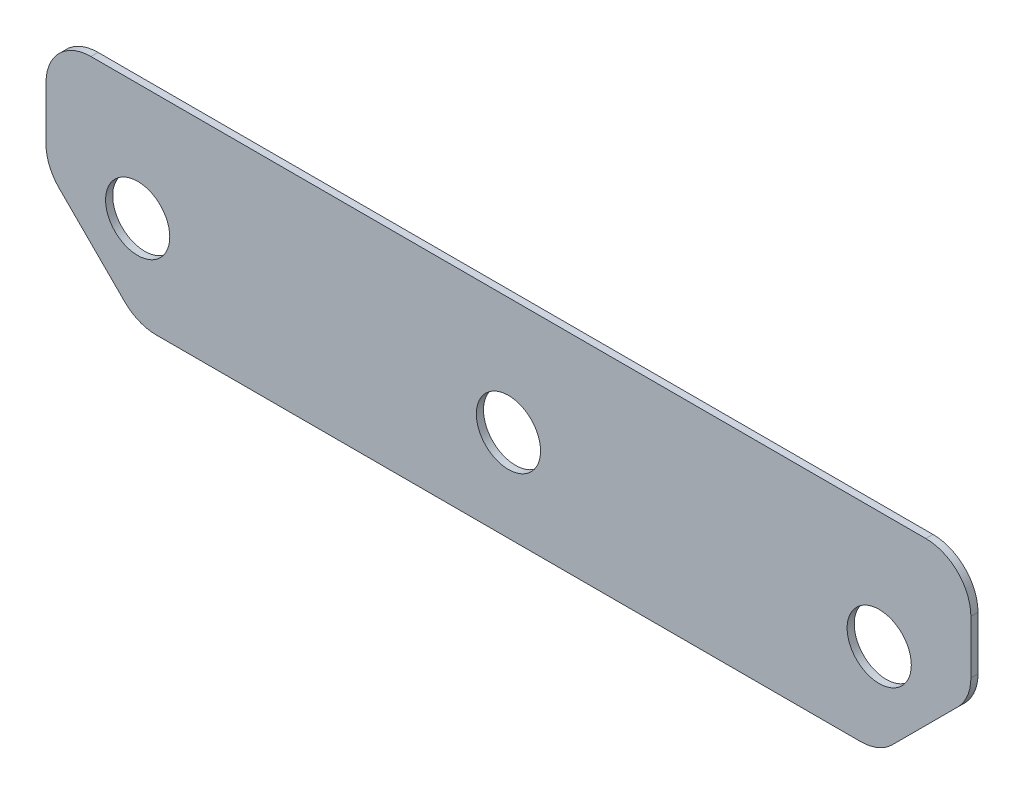
SolidWorks part; units mm, degrees
ref_plane "Front Plane" through (0, 0, 0) normal (0, 0, 1) x (1, 0, 0)
ref_plane "Top Plane" through (0, 0, 0) normal (0, 1, 0) x (1, 0, 0)
ref_plane "Right Plane" through (0, 0, 0) normal (1, 0, 0) x (0, 0, -1)
sketch "Sketch1" plane through (0, 0, 0) normal (0, 0, 1) x (1, 0, 0)
  line L0 (-165.0238, -40.8) -> (165.0238, -40.8)
  line L1 (-205.8238, 0) -> (-205.8238, 52)
  line L2 (-205.8238, 52) -> (205.8238, 52)
  line L3 (205.8238, 52) -> (205.8238, 0)
  line L4 (205.8238, 0) -> (165.0238, -40.8)
  line L5 (-205.8238, 0) -> (-165.0238, -40.8)
  circle A0 centre (0, 0) radius 50.8
  circle A1 centre (165.0238, 0) radius 50.8
  circle A2 centre (-165.0238, 0) radius 50.8
  arc A3 (-165.0238, -40.8) -> (-205.8238, 0) centre (-165.0238, 0) ccw
  arc A4 (205.8238, 0) -> (165.0238, -40.8) centre (165.0238, 0) ccw
  circle A5 centre (-165.0238, 0) radius 40.8 construction
  circle A6 centre (165.0238, 0) radius 40.8 construction
  circle A7 centre (-165.0238, 0) radius 14.2875
  circle A8 centre (0, 0) radius 14.2875
  circle A9 centre (165.0238, 0) radius 14.2875
  dimension "D1" = 101.6
  dimension "D2" = 101.6
  dimension "D4" = 101.6
  dimension "D6" = 10
  dimension "D9" = 28.575
  dimension "D10" = 28.575
  dimension "D11" = 28.575
  dimension "D3" = 165.0238
  dimension "D5" = 165.0238
  dimension "D8" = 52
  dimension "D7" = 10
extrude "Boss-Extrude1" add sketch "Sketch1" along normal blind 3.175 contours L5 A3 A7 | A3 L0 A2 L1 | A2 L0 A0 A1 L3 L2 L1 | L0 A0 A8 | L4 A4 A9 | A4 L3 A1 L0
fillet "Fillet1" radius 20 2 edges at (-205.8238, 52, 1.5875) (205.8238, 52, 1.5875)
fillet "Fillet2" radius 20 4 edges at (-205.8238, 0, 1.5875) (-165.0238, -40.8, 1.5875) (165.0238, -40.8, 1.5875) (205.8238, 0, 1.5875)
